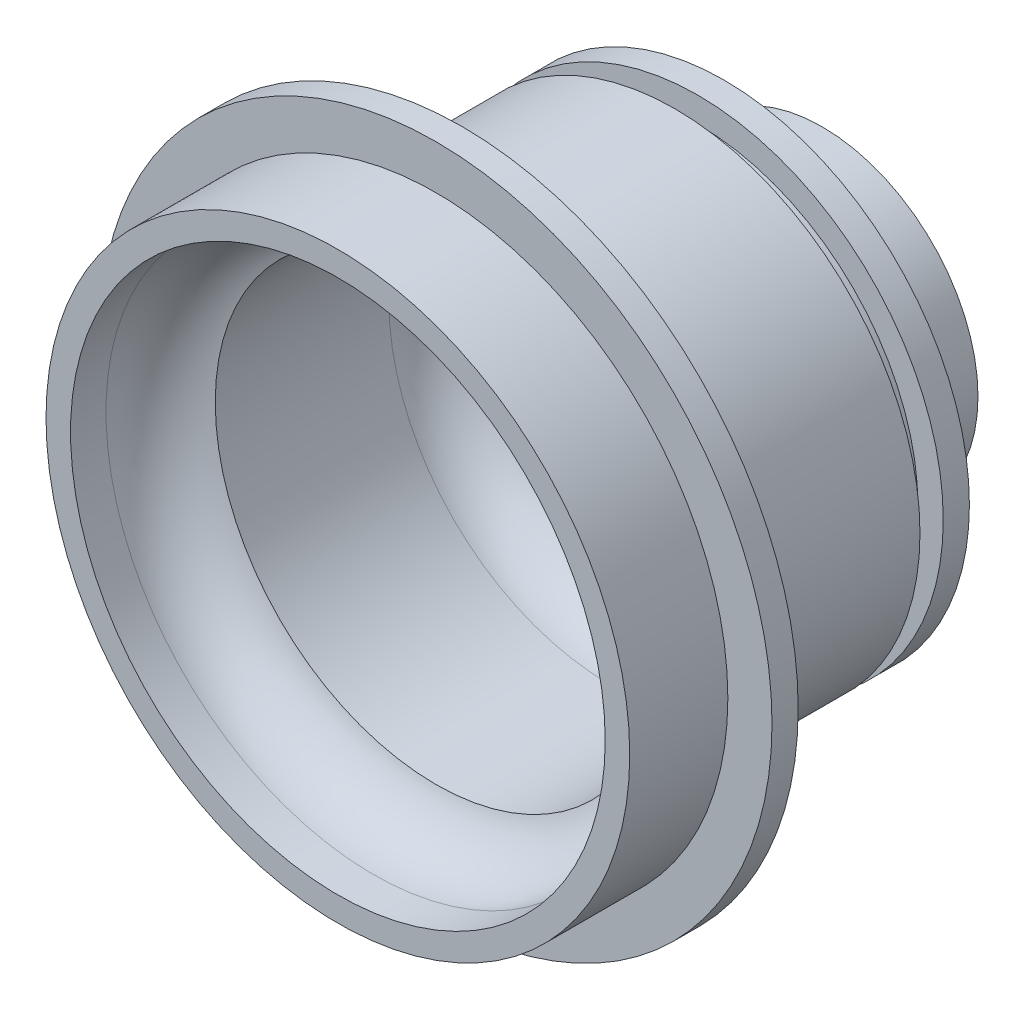
SolidWorks part; units mm, degrees
material "ASTM A36 Steel"
ref_plane "Front Plane" through (0, 0, 0) normal (0, 0, 1) x (1, 0, 0)
ref_plane "Top Plane" through (0, 0, 0) normal (0, 1, 0) x (1, 0, 0)
ref_plane "Right Plane" through (0, 0, 0) normal (1, 0, 0) x (0, 0, -1)
sketch "Sketch2" plane through (0, 0, 0) normal (1, 0, 0) x (0, 0, -1)
  line L0 (-74.8044, 0) -> (74.8044, 0) construction
  line L1 (15.5224, 9.525) -> (9.5224, 9.525)
  line L2 (9.5224, 9.525) -> (9.5224, 15)
  line L3 (9.5224, 15) -> (7.9224, 15)
  line L4 (7.9224, 15) -> (7.9224, 13.45)
  line L5 (7.9224, 13.45) -> (6.5, 13.45)
  line L6 (6.5, 13.45) -> (6.5, 15)
  line L7 (6.5, 15) -> (-6.5, 15)
  line L8 (-6.5, 15) -> (-6.5, 20.55)
  line L9 (-6.5, 20.55) -> (-8.1, 20.55)
  line L10 (-8.1, 20.55) -> (-8.1, 17.85)
  line L11 (-8.1, 17.85) -> (-14.1, 17.85)
  line L12 (-14.1, 17.85) -> (-14.1, 16.35)
  line L13 (8.5224, 6.525) -> (15.5224, 6.525)
  line L14 (15.5224, 6.525) -> (15.5224, 9.525)
  line L15 (-8.1, 13.5) -> (2.5224, 13.5)
  line L17 (-11.9311, 16.35) -> (-14.1, 16.35)
  line L18 (6.5224, 9.5) -> (6.5224, 8.525)
  arc A0 (2.5224, 13.5) -> (6.5224, 9.5) centre (2.5224, 9.5) cw
  arc A1 (8.5224, 6.525) -> (6.5224, 8.525) centre (8.5224, 8.525) cw
  arc A2 (-11.9311, 16.35) -> (-8.1, 13.5) centre (-11.9311, 12.35) cw
  point P24 (0, 15)
  dimension "D13" = 4
  dimension "D14" = 2
  dimension "D17" = 4
  dimension "D1" = 19.05
  dimension "D2" = 3
  dimension "D3" = 6
  dimension "D4" = 1.6
  dimension "D5" = 13
  dimension "D6" = 30
  dimension "D7" = 2.7
  dimension "D8" = 35.7
  dimension "D9" = 1.6
  dimension "D10" = 6
  dimension "D11" = 1.5
  dimension "D12" = 3
  dimension "D15" = 26.9
  dimension "D16" = 1.4224
  dimension "D18" = 1.5
revolve "Revolve1" add sketch "Sketch2" angle 360 about L0
fillet "Fillet2" radius 2 1 edges at (9.525, 0, -9.5224)
